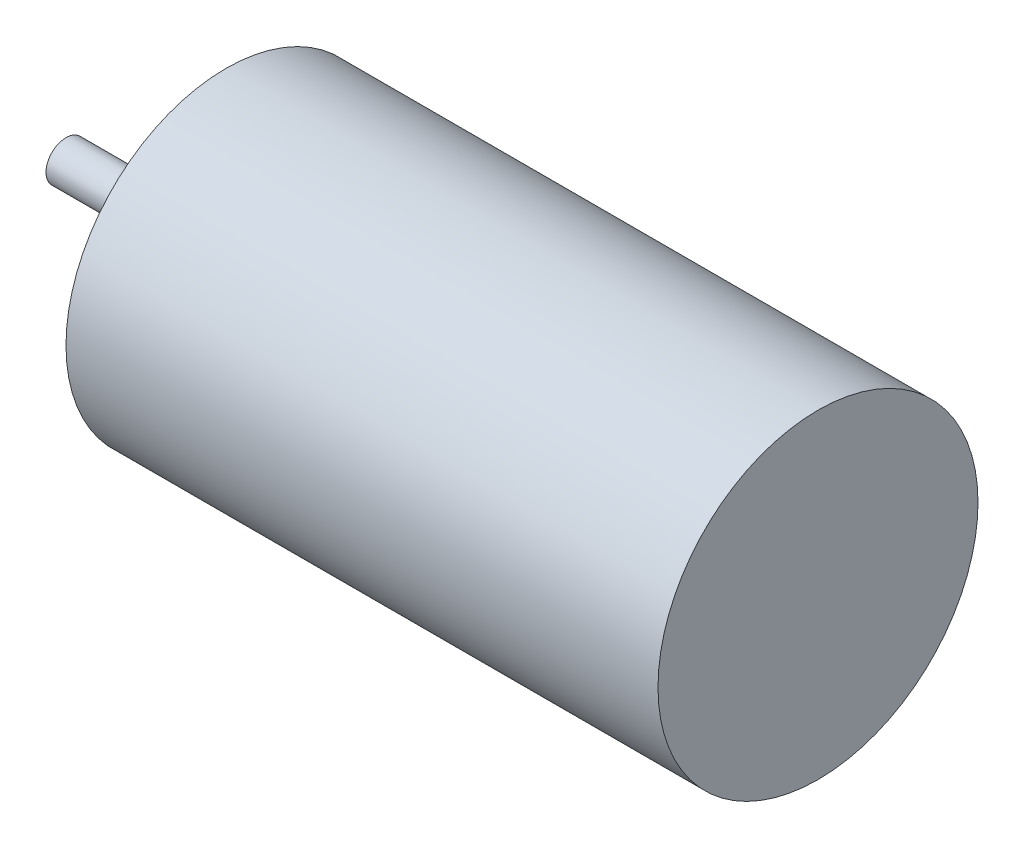
SolidWorks part; units mm, degrees
material "Orange anodized aluminum"
ref_plane "Front Plane" through (0, 0, 0) normal (0, 0, 1) x (1, 0, 0)
ref_plane "Top Plane" through (0, 0, 0) normal (0, 1, 0) x (1, 0, 0)
ref_plane "Right Plane" through (0, 0, 0) normal (1, 0, 0) x (0, 0, -1)
sketch "Sketch1" plane through (0, 0, 0) normal (1, 0, 0) x (0, 0, -1)
  circle A0 centre (0, 0) radius 20
  dimension "D1" = 40
extrude "Boss-Extrude1" add sketch "Sketch1" along normal blind 74
sketch "Sketch2" plane through (0, 0, 0) normal (-1, 0, 0) x (0, 0, 1)
  circle A0 centre (0, 0) radius 2.5
extrude "Boss-Extrude2" add sketch "Sketch2" along normal blind 20
